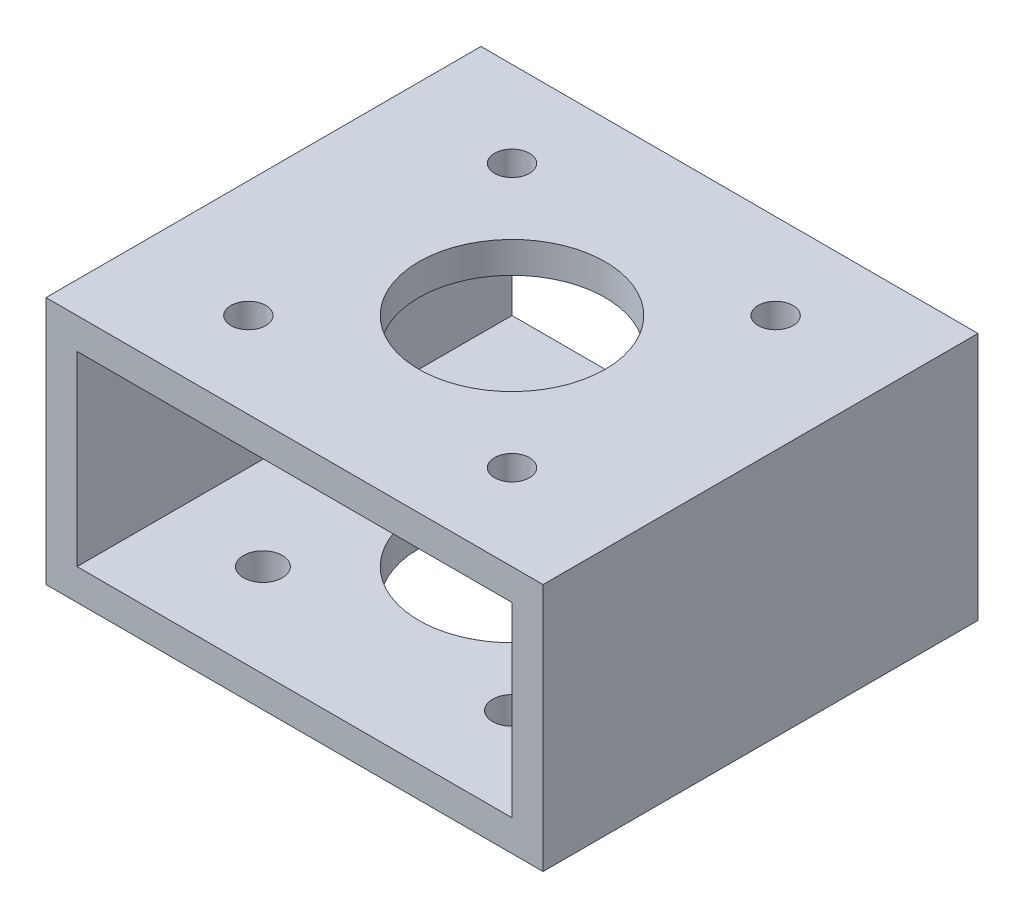
SolidWorks part; units mm, degrees
ref_plane "Front Plane" through (0, 0, 0) normal (0, 0, 1) x (1, 0, 0)
ref_plane "Top Plane" through (0, 0, 0) normal (0, 1, 0) x (1, 0, 0)
ref_plane "Right Plane" through (0, 0, 0) normal (1, 0, 0) x (0, 0, -1)
sketch "Sketch1" plane through (0, 0, 0) normal (0, 0, 1) x (1, 0, 0)
  line L10 (-25.4, 25.4) -> (25.4, 25.4)
  line L11 (-25.4, 25.4) -> (-25.4, 0)
  line L12 (-25.4, 0) -> (25.4, 0)
  line L13 (25.4, 25.4) -> (25.4, 0)
  point P6 (0, 0)
  dimension "D1" = 50.8
  dimension "D2" = 25.4
extrude "Boss-Extrude1" add sketch "Sketch1" along normal mid plane 44.45
sketch "Sketch2" plane through (0, 25.4, 0) normal (0, 1, 0) x (1, 0, 0)
  circle A0 centre (0, 0) radius 9.525
  circle A1 centre (0, 0) radius 18 construction
  dimension "D1" = 19.05
  dimension "D2" = 36
extrude "Cut-Extrude1" cut sketch "Sketch2" against normal through all contours A0
sketch "Sketch4" plane through (0, 0, -22.225) normal (0, 0, -1) x (-1, 0, 0)
  line L0 (0, 0) -> (0, 25.4) construction
  line L1 (-25.4, 25.4) -> (25.4, 25.4) construction
  line L2 (25.4, 0) -> (-25.4, 0) construction
  line L3 (22.225, 3.175) -> (-22.225, 3.175)
  line L4 (22.225, 3.175) -> (22.225, 22.225)
  line L5 (22.225, 22.225) -> (-22.225, 22.225)
  line L6 (-22.225, 3.175) -> (-22.225, 22.225)
  line L7 (-25.4, 0) -> (-25.4, 25.4) construction
  line L8 (25.4, 25.4) -> (25.4, 0) construction
  dimension "D1" = 3.175
  dimension "D2" = 3.175
  dimension "D3" = 3.175
  dimension "D4" = 3.175
extrude "Cut-Extrude3" cut sketch "Sketch4" against normal through all
sketch "Holes for channel" plane through (0, 25.4, 0) normal (0, 1, 0) x (1, 0, 0)
  line L0 (0, 0) -> (19.05, 0) construction
  line L1 (-13.4704, -13.4704) -> (13.4704, 13.4704) construction
  line L2 (13.4704, -13.4704) -> (-13.4704, 13.4704) construction
  circle A0 centre (0, 0) radius 19.05 construction
  dimension "D1" = 38.1
  dimension "D2" = 45
  dimension "D3" = 45
sketch "Pattern for valve" plane through (0, 0, 0) normal (0, -1, 0) x (1, 0, 0)
  line L0 (0, 0) -> (18, 0) construction
  line L1 (-12.7279, -12.7279) -> (12.7279, 12.7279) construction
  line L2 (12.7279, -12.7279) -> (-12.7279, 12.7279) construction
  circle A0 centre (0, 0) radius 18 construction
  dimension "D1" = 36
  dimension "D2" = 45
  dimension "D3" = 45
hole_wizard "9/64 (0.14063) Diameter Hole2" positions "Sketch5" profile "Sketch6" hole size "9/64" standard "ANSI Inch" end condition up to next
sketch "Sketch5" plane through (0, 25.4, 0) normal (0, 1, 0) x (1, 0, 0)
  point P0 (-13.4704, 13.4704)
  point P3 (13.4704, 13.4704)
  point P6 (13.4704, -13.4704)
  point P9 (-13.4704, -13.4704)
sketch "Sketch6" plane through (-13.4704, 25.4, -13.4704) normal (1, 0, 0) x (0, 0, 1)
  line L0 (0, 0) -> (0, 3.175)
  line L1 (0, 3.175) -> (1.786, 3.175)
  line L2 (1.786, 3.175) -> (1.786, 0)
  line L5 (1.786, 0) -> (0, 0)
  line L11 (0, -6.35) -> (0, 107.95) construction
  dimension "Thru Hole Dia." = 3.572
  dimension "Thru Hole Depth" = 3.175
hole_wizard "5/32 (0.15625) Diameter Hole1" positions "Sketch7" profile "Sketch8" hole size "5/32" standard "ANSI Inch" end condition up to next
sketch "Sketch7" plane through (0, 0, 0) normal (0, -1, 0) x (-1, 0, 0)
  point P0 (-12.7279, 12.7279)
  point P3 (12.7279, 12.7279)
  point P6 (12.7279, -12.7279)
  point P9 (-12.7279, -12.7279)
sketch "Sketch8" plane through (12.7279, 0, -12.7279) normal (1, 0, 0) x (0, 0, -1)
  line L0 (0, 0) -> (0, 3.175)
  line L1 (0, 3.175) -> (1.9844, 3.175)
  line L2 (1.9844, 3.175) -> (1.9844, 0)
  line L5 (1.9844, 0) -> (0, 0)
  line L11 (0, -6.35) -> (0, 107.95) construction
  dimension "Thru Hole Dia." = 3.9688
  dimension "Thru Hole Depth" = 3.175
